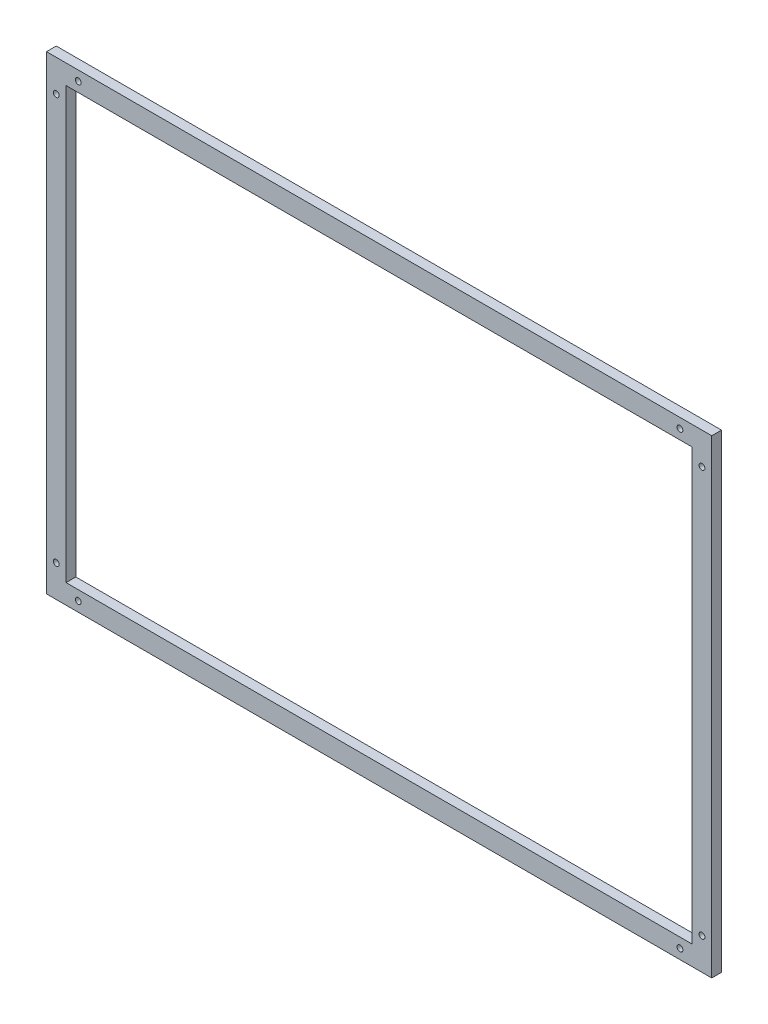
SolidWorks part; units mm, degrees
ref_plane "Plan de face" through (0, 0, 0) normal (0, 0, 1) x (1, 0, 0)
ref_plane "Plan de dessus" through (0, 0, 0) normal (0, 1, 0) x (1, 0, 0)
ref_plane "Plan de droite" through (0, 0, 0) normal (1, 0, 0) x (0, 0, -1)
sketch "Esquisse1" plane through (0, 0, 0) normal (0, 0, 1) x (1, 0, 0)
  line L1 (0, 0) -> (-680, 0)
  line L2 (0, 0) -> (0, 480)
  line L3 (0, 480) -> (-680, 480)
  line L4 (-680, 0) -> (-680, 480)
  line L5 (-660, 460) -> (-20, 460)
  line L6 (-660, 460) -> (-660, 20)
  line L7 (-660, 20) -> (-20, 20)
  line L8 (-20, 460) -> (-20, 20)
  dimension "D1" = 680
  dimension "D2" = 480
  dimension "D3" = 20
  dimension "D4" = 20
  dimension "D5" = 20
  dimension "D6" = 20
extrude "Boss.-Extru.1" add sketch "Esquisse1" along normal blind 10
sketch "Esquisse2" plane through (0, 0, 10) normal (0, 0, 1) x (1, 0, 0)
  line L0 (0, 0) -> (0, 480) construction
  line L1 (0, 480) -> (-680, 480) construction
  line L2 (-20, 460) -> (-660, 460) construction
  line L3 (-680, 0) -> (0, 0) construction
  line L4 (-660, 20) -> (-20, 20) construction
  line L5 (-680, 480) -> (-680, 0) construction
  line L6 (-660, 460) -> (-660, 20) construction
  circle A0 centre (-32.5, 470) radius 3
  circle A1 centre (-10, 447.5) radius 3
  circle A2 centre (-647.5, 470) radius 3
  circle A3 centre (-670, 447.5) radius 3
  circle A4 centre (-670, 32.5) radius 3
  circle A5 centre (-647.5, 10) radius 3
  circle A6 centre (-32.5, 10) radius 3
  circle A7 centre (-10, 32.5) radius 3
  dimension "D1" = 6
  dimension "D2" = 6
  dimension "D3" = 32.5
  dimension "D4" = 32.5
  dimension "D5" = 10
  dimension "D6" = 10
  dimension "D7" = 6
  dimension "D8" = 6
  dimension "D9" = 32.5
  dimension "D10" = 32.5
  dimension "D11" = 10
  dimension "D12" = 10
  dimension "D13" = 6
  dimension "D14" = 32.5
  dimension "D15" = 32.5
  dimension "D16" = 6
  dimension "D17" = 10
  dimension "D18" = 10
  dimension "D19" = 6
  dimension "D20" = 6
  dimension "D21" = 10
  dimension "D22" = 10
  dimension "D23" = 32.5
  dimension "D24" = 32.5
extrude "Enlèv. mat.-Extru.1" cut sketch "Esquisse2" against normal through all
